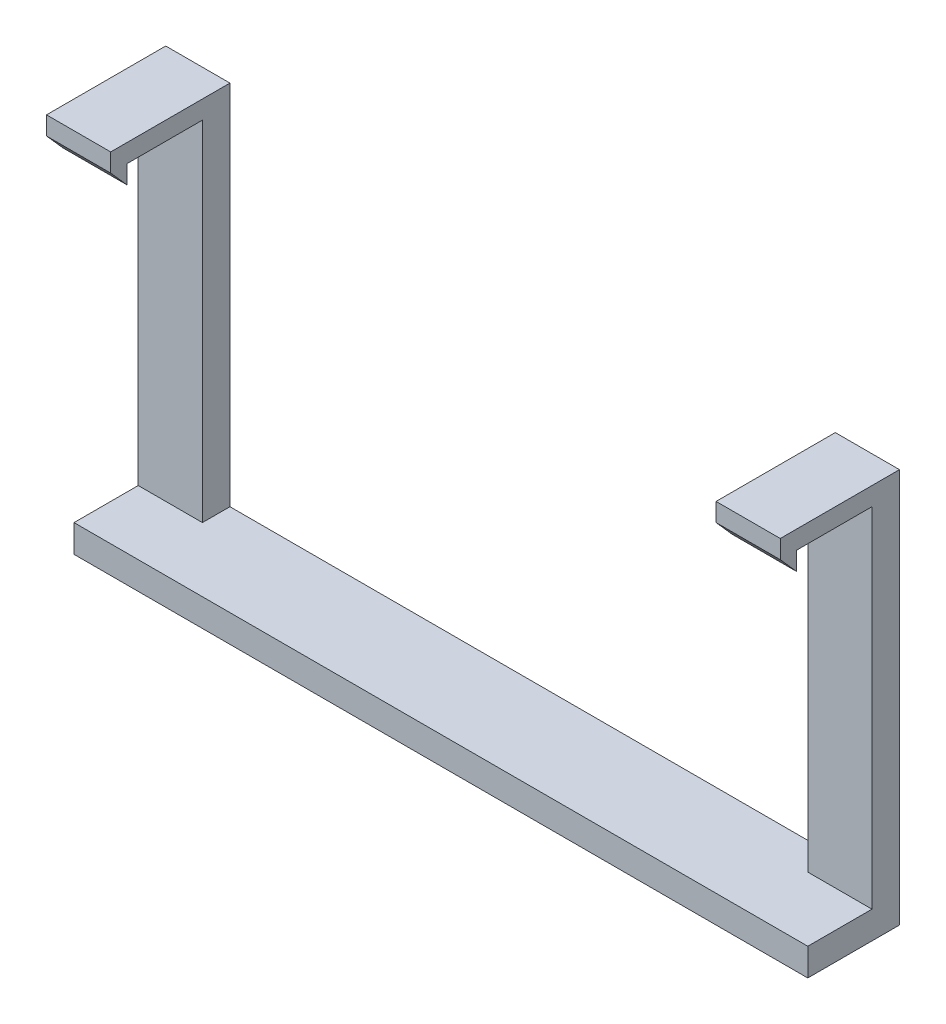
SolidWorks part; units mm, degrees
ref_plane "Front Plane" through (0, 0, 0) normal (0, 0, 1) x (1, 0, 0)
ref_plane "Top Plane" through (0, 0, 0) normal (0, 1, 0) x (1, 0, 0)
ref_plane "Right Plane" through (0, 0, 0) normal (1, 0, 0) x (0, 0, -1)
sketch "Sketch1" plane through (0, 0, 0) normal (0, 0, 1) x (1, 0, 0)
  line L0 (0, 0) -> (40, 0)
  line L1 (40, 0) -> (40, 43)
  line L2 (0, 0) -> (0, 3)
  line L3 (0, 3) -> (33, 3)
  line L4 (33, 3) -> (33, 43)
  line L5 (33, 43) -> (40, 43)
  dimension "D1" = 40
  dimension "D2" = 43
  dimension "D3" = 7
  dimension "D4" = 3
extrude "Boss-Extrude1" add sketch "Sketch1" along normal blind 13
sketch "Sketch2" plane through (40, 0, 0) normal (1, 0, 0) x (0, 0, -1)
  line L0 (-13, 43) -> (-13, 41)
  line L1 (-13, 0) -> (-13, 43) construction
  line L2 (-11.2294, 41.002) -> (-3, 41.002)
  line L3 (-3, 41.002) -> (-3, 3)
  line L4 (-3, 3) -> (-10, 3)
  line L5 (-10, 3) -> (-10, 0)
  line L6 (-13, 0) -> (0, 0) construction
  line L7 (-10, 0) -> (0, 0)
  line L8 (0, 0) -> (0, 43)
  line L9 (0, 43) -> (-13, 43)
  line L12 (-11.2294, 41.002) -> (-11.2294, 39.002)
  line L13 (-11.2294, 39.002) -> (-13, 41)
  line L14 (-13, 41) -> (-13, 0)
  line L15 (-13, 0) -> (-10, 0)
  point P5 (0, 0)
  point P20 (0, 0)
  line M15 (-13, 43) -> (-13, 0)
  line M16 (-13, 0) -> (0, 0)
  dimension "D1" = 2
  dimension "D2" = 3
  dimension "D3" = 3
  dimension "D4" = 10
  dimension "D5" = 2.6696
  dimension "D6" = 2
  dimension "D7" = 1.7706
extrude "Cut-Extrude1" cut sketch "Sketch2" against normal blind 100 contours L12 L13 L5 L4 L3 L2 M15 M16
mirror "Mirror2" about plane through (0, 0, 13) normal (1, 0, 0) of bodies 103
